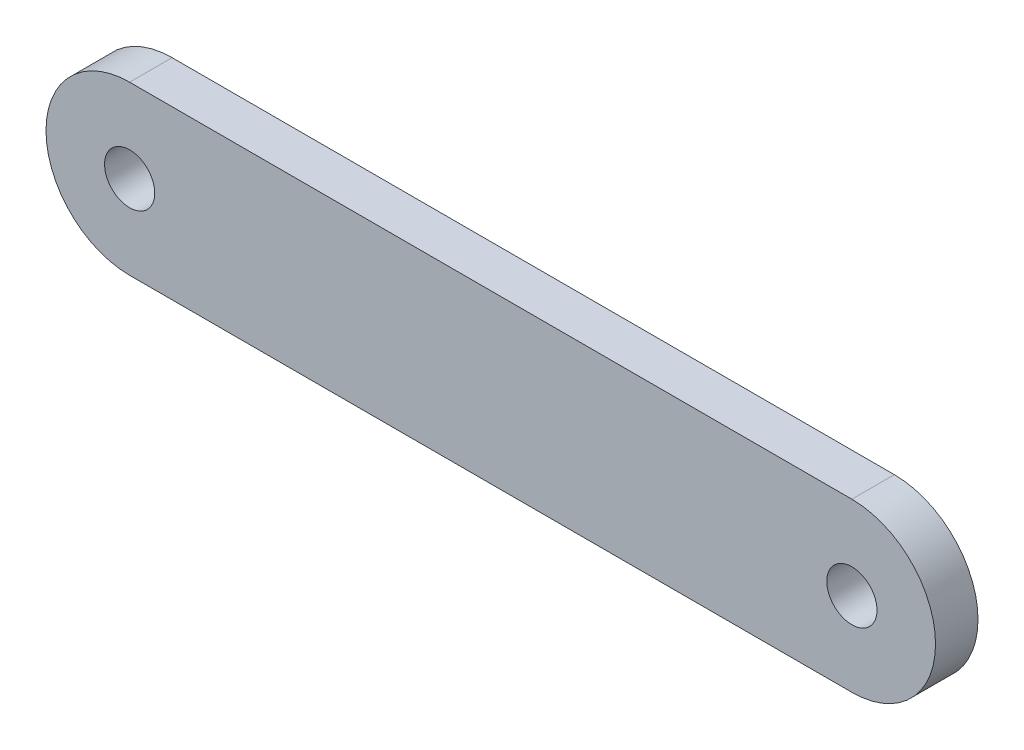
SolidWorks part; units mm, degrees
ref_plane "前基準面" through (0, 0, 0) normal (0, 0, 1) x (1, 0, 0)
ref_plane "上基準面" through (0, 0, 0) normal (0, 1, 0) x (1, 0, 0)
ref_plane "右基準面" through (0, 0, 0) normal (1, 0, 0) x (0, 0, -1)
sketch "草圖2" plane through (0, 0, 0) normal (0, 0, 1) x (1, 0, 0)
  line L0 (-10.795, 0) -> (10.795, 0) construction
  line L1 (-10.795, 0) -> (10.795, 0) construction
  line L2 (-10.795, 2.5) -> (10.795, 2.5)
  line L3 (-10.795, -2.5) -> (10.795, -2.5)
  arc A0 (-10.795, 2.5) -> (-10.795, -2.5) centre (-10.795, 0) ccw
  arc A1 (10.795, -2.5) -> (10.795, 2.5) centre (10.795, 0) ccw
  circle A2 centre (-10.795, 0) radius 0.75
  circle A3 centre (10.795, 0) radius 0.75
  point P3 (0, 0)
  point P4 (0, 0)
  dimension "D2" = 2.5
  dimension "D3" = 1.5
  dimension "D1" = 21.59
extrude "填料-伸長1" add sketch "草圖2" along normal mid plane 1.27
